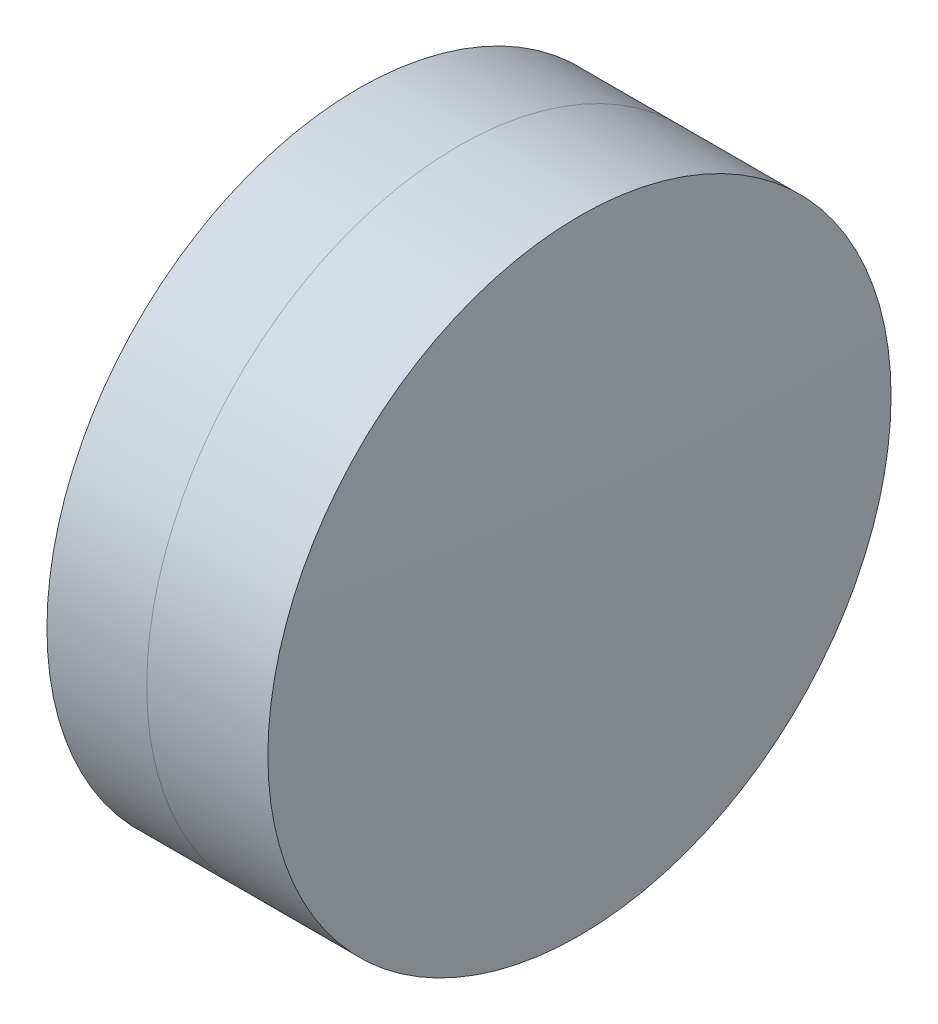
SolidWorks part; units mm, degrees
ref_plane "前视基准面" through (0, 0, 0) normal (0, 0, 1) x (1, 0, 0)
ref_plane "上视基准面" through (0, 0, 0) normal (0, 1, 0) x (1, 0, 0)
ref_plane "右视基准面" through (0, 0, 0) normal (1, 0, 0) x (0, 0, -1)
sketch "草图1" plane through (0, 0, 0) normal (0, 1, 0) x (1, 0, 0)
  line L0 (-9.7026, 0) -> (11.7646, 0) construction
  line L1 (6.9576, -5) -> (8.5588, -5)
  line L2 (6.9576, 5) -> (8.5588, 5)
  arc A0 (8.5588, -5) -> (8.5588, 5) centre (-16.3126, 0) ccw
  arc A1 (6.9576, 5) -> (6.9576, -5) centre (45.7204, 0) ccw
  point P10 (6.6364, 0)
  point P11 (9.0564, 0)
  dimension "D3" = 39.084
  dimension "D4" = 25.369
  dimension "D1" = 5
  dimension "D2" = 5
  dimension "D5" = 2.42
revolve "旋转1" add sketch "草图1" angle 360 about L0
sketch "草图2" plane through (0, 0, 0) normal (0, 1, 0) x (1, 0, 0)
  line L0 (-0.5519, 0) -> (13.3053, 0) construction
  line L2 (8.5588, 5) -> (10.5032, 5)
  line L3 (8.5588, -5) -> (10.5032, -5)
  arc A0 (10.5032, -5) -> (10.5032, 5) centre (-70.9716, 0) ccw
  arc A1 (8.5588, -5) -> (8.5588, 5) centre (-16.3126, 0) ccw construction
  arc A2 (8.5588, -5) -> (8.5588, 5) centre (-16.3126, 0) ccw
  point P4 (9.0564, 0)
  point P8 (10.6564, 0)
  dimension "D1" = 81.628
  dimension "D2" = 1.6
revolve "旋转3" add sketch "草图2" angle 360 about L0
